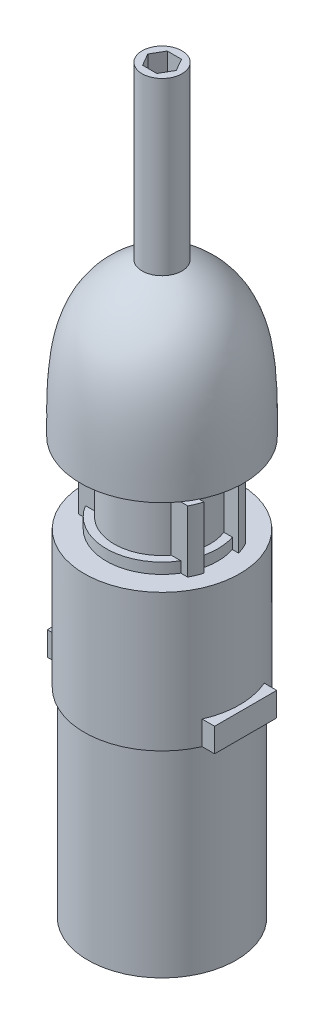
SolidWorks part; units mm, degrees
ref_plane "Front Plane" through (0, 0, 0) normal (0, 0, 1) x (1, 0, 0)
ref_plane "Top Plane" through (0, 0, 0) normal (0, 1, 0) x (1, 0, 0)
ref_plane "Right Plane" through (0, 0, 0) normal (1, 0, 0) x (0, 0, -1)
sketch "Sketch1" plane through (0, 0, 0) normal (0, 1, 0) x (1, 0, 0)
  circle A0 centre (0, 0) radius 14
  dimension "D1" = 28
extrude "Boss-Extrude1" add sketch "Sketch1" along normal blind 2.7
sketch "Sketch2" plane through (0, 0, 0) normal (0, 1, 0) x (1, 0, 0)
  circle A0 centre (0, 0) radius 12
  dimension "D1" = 24
extrude "Boss-Extrude2" add sketch "Sketch2" along normal blind 15.5
sketch "Sketch3" plane through (0, 0, 0) normal (0, 1, 0) x (1, 0, 0)
  line L0 (13.6999, 7.25) -> (-13.6999, 7.25)
  line L1 (-15.5, -7.25) -> (15.5, -7.25) construction
  line L2 (-15.5, -7.25) -> (-15.5, 7.25) construction
  line L3 (-15.5, 7.25) -> (15.5, 7.25) construction
  line L4 (15.5, -7.25) -> (15.5, 7.25) construction
  line L5 (-15.5, -7.25) -> (15.5, 7.25) construction
  line L6 (-15.5, 7.25) -> (15.5, -7.25) construction
  line L7 (-15.5, -4.35) -> (15.5, -4.35) construction
  line L8 (-15.5, -4.35) -> (-15.5, 4.35) construction
  line L9 (-15.5, 4.35) -> (15.5, 4.35) construction
  line L10 (15.5, -4.35) -> (15.5, 4.35) construction
  line L11 (-15.5, -4.35) -> (15.5, 4.35) construction
  line L12 (-15.5, 4.35) -> (15.5, -4.35) construction
  line L13 (14.8771, 4.35) -> (-14.8771, 4.35)
  line L14 (14.8771, -4.35) -> (-14.8771, -4.35)
  line L15 (13.6999, -7.25) -> (-13.6999, -7.25)
  circle A0 centre (0, 0) radius 15.5 construction
  arc A1 (-14.8771, 4.35) -> (-13.6999, 7.25) centre (0, 0) cw
  arc A2 (13.6999, 7.25) -> (14.8771, 4.35) centre (0, 0) cw
  arc A3 (14.8771, -4.35) -> (13.6999, -7.25) centre (0, 0) cw
  arc A4 (-13.6999, -7.25) -> (-14.8771, -4.35) centre (0, 0) cw
  point P0 (0, 0)
  point P5 (0, 0)
  point P24 (-14.837, -4.35)
  dimension "D1" = 14.5
  dimension "D2" = 31
  dimension "D3" = 8.7
extrude "Boss-Extrude3" add sketch "Sketch3" along normal blind 15.5 contours A2 L0 A1 L13 | A4 L15 A3 L14
sketch "Sketch4" plane through (0, 0, 0) normal (0, -1, 0) x (1, 0, 0)
  circle A0 centre (0, 0) radius 19.5
  dimension "D1" = 39
extrude "Boss-Extrude4" add sketch "Sketch4" along normal blind 34.5
sketch "Sketch5" plane through (0, -34.5, 0) normal (0, -1, 0) x (1, 0, 0)
  line L1 (-21, -7.8) -> (21, -7.8)
  line L2 (-21, -7.8) -> (-21, 7.8)
  line L3 (-21, 7.8) -> (21, 7.8)
  line L4 (21, -7.8) -> (21, 7.8)
  line L5 (-21, -7.8) -> (21, 7.8) construction
  line L6 (-21, 7.8) -> (21, -7.8) construction
  point P0 (0, 0)
  dimension "D1" = 15.6
  dimension "D2" = 42
extrude "Boss-Extrude5" add sketch "Sketch5" against normal blind 6
sketch "Sketch6" plane through (0, -34.5, 0) normal (0, -1, 0) x (1, 0, 0)
  circle A0 centre (0, 0) radius 18.6
  dimension "D1" = 37.2
extrude "Boss-Extrude6" add sketch "Sketch6" along normal blind 50 separate body
sketch "Sketch7" plane through (0, 0, 0) normal (0, 0, 1) x (1, 0, 0)
  line L2 (0, 15.5) -> (0, 20.2)
  line L3 (0, 20.2) -> (0, 101.5)
  line L4 (0, 101.5) -> (5, 101.5)
  line L5 (5, 101.5) -> (5, 58.6)
  line L6 (0, 15.5) -> (7.5, 15.5)
  line L7 (7.5, 15.5) -> (7.5, 20.2)
  line L8 (7.5, 20.2) -> (20.5, 20.2)
  line L9 (16, 49.2) -> (16, 20.2) construction
  line L10 (16, 49.2) -> (0, 49.2) construction
  spline S0 degree 3 poles (20.5, 20.2) (20.4745, 37.4327) (20.8661, 50.9965) (5, 58.6) knots 0 0 0 0 1 1 1 1
  dimension "D1" = 4.7
  dimension "D2" = 81.3
  dimension "D3" = 5
  dimension "D4" = 42.9
  dimension "D5" = 7.5
  dimension "D6" = 20.5
  dimension "D7" = 29
  dimension "D8" = 16
revolve "Revolve1" add sketch "Sketch7" angle 360 about L3
sketch "Sketch8" plane through (0, 0, 0) normal (0, 0, 1) x (1, 0, 0)
  line L0 (5, 58.6) -> (-5, 58.6) construction
  line L1 (5, 58.6) -> (-5, 58.6)
split "Split1" trim tools "Sketch8" bodies to split 107 resulting bodies 108 109
sketch "Sketch9" plane through (0, 101.5, 0) normal (0, 1, 0) x (1, 0, 0)
  line L1 (3.5796, 0) -> (1.7898, 3.1)
  line L2 (1.7898, 3.1) -> (-1.7898, 3.1)
  line L3 (-1.7898, 3.1) -> (-3.5796, 0)
  line L4 (-3.5796, 0) -> (-1.7898, -3.1)
  line L5 (-1.7898, -3.1) -> (1.7898, -3.1)
  line L6 (1.7898, -3.1) -> (3.5796, 0)
  circle A0 centre (0, 0) radius 3.1 construction
extrude "Cut-Extrude1" cut sketch "Sketch9" against normal blind 11.2
equation "\"m3_hole\"= 3.5"
equation "\"m3_washer\"= 7.3"
equation "\"m3_nut\"= 5.3"
equation "\"guide_width\"= 10.0"
equation "\"guide_length\"= 65.0"
equation "\"guide_tab_length\" = 10.0"
equation "\"guide_tab_width\" = 9.0"
equation "\"guide_thickness\" = 12.0"
equation "\"grinder_od\"= 52.0"
equation "\"grinder_id\"= 45.5"
equation "\"grinder_adjust_od\" = 58.0"
equation "\"funnel_width_from_adjust_ring\" = 13.0"
equation "\"drill_contact_diameter_small\" = 24.0"
equation "\"drill_contact_diameter_medium\" = 28.0"
equation "\"drill_contact_diameter_large\" = 39.0"
equation "\"drill_contact_diameter_tab\" = 31.0"
equation "\"D1@Sketch2\"=\"drill_contact_diameter_small\""
equation "\"D1@Sketch1\"=\"drill_contact_diameter_medium\""
equation "\"D2@Sketch3\"=\"drill_contact_diameter_tab\""
equation "\"drill_contact_ow_tab\" = 14.5"
equation "\"drill_contact_iw_tab\" = 8.7"
equation "\"D3@Sketch3\"=\"drill_contact_iw_tab\""
equation "\"D1@Sketch3\"=\"drill_contact_ow_tab\""
equation "\"drill_contact_small_height\" = 15.5"
equation "\"D1@Boss-Extrude3\"=\"drill_contact_small_height\""
equation "\"drill_contact_large_height\" = 34.5"
